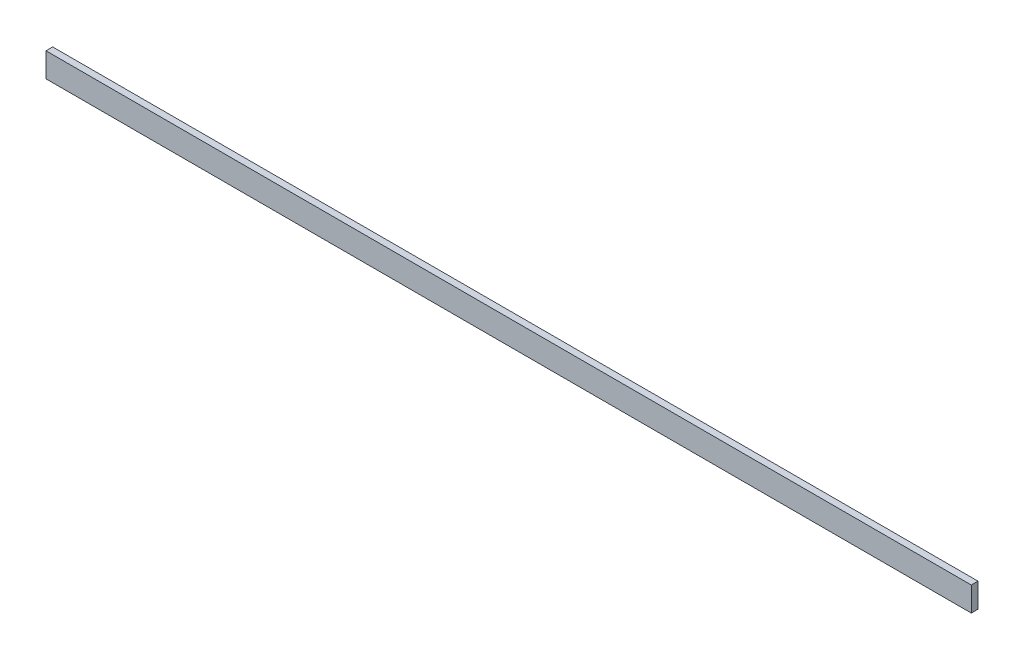
SolidWorks part; units mm, degrees
ref_plane "Plan de face" through (0, 0, 0) normal (0, 0, 1) x (1, 0, 0)
ref_plane "Plan de dessus" through (0, 0, 0) normal (0, 1, 0) x (1, 0, 0)
ref_plane "Plan de droite" through (0, 0, 0) normal (1, 0, 0) x (0, 0, -1)
sketch "Esquisse1" plane through (0, 0, 0) normal (0, 0, 1) x (1, 0, 0)
  line L1 (0, 0) -> (3044, 0)
  line L2 (0, 0) -> (0, 80)
  line L3 (0, 80) -> (3044, 80)
  line L4 (3044, 0) -> (3044, 80)
  dimension "D1" = 3044
  dimension "D2" = 80
extrude "Extrusion1" add sketch "Esquisse1" along normal blind 22
